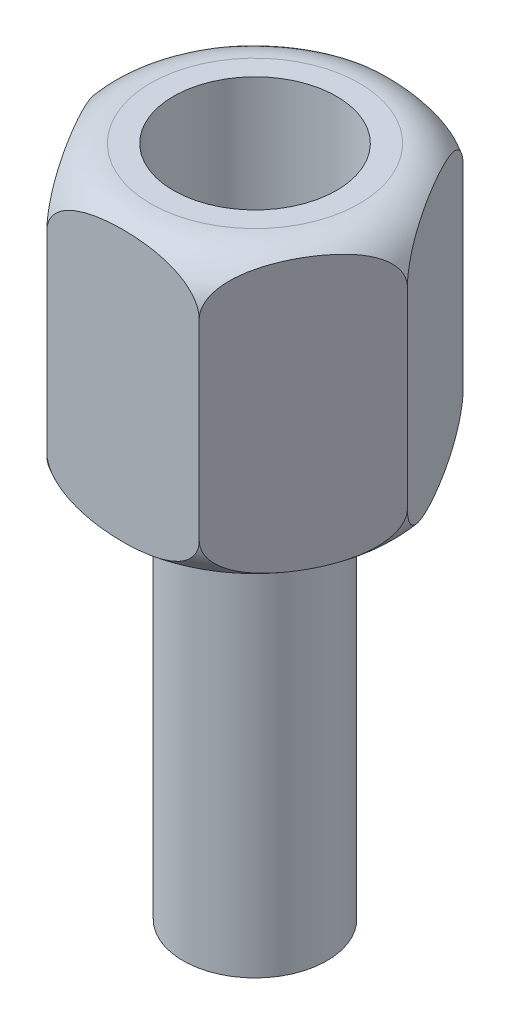
SolidWorks part; units mm, degrees
material "Brass"
ref_plane "Front Plane" through (0, 0, 0) normal (0, 0, 1) x (1, 0, 0)
ref_plane "Top Plane" through (0, 0, 0) normal (0, 1, 0) x (1, 0, 0)
ref_plane "Right Plane" through (0, 0, 0) normal (1, 0, 0) x (0, 0, -1)
sketch "Sketch1" plane through (0, 0, 0) normal (0, 1, 0) x (1, 0, 0)
  line L1 (3.1754, 0) -> (1.5877, 2.75)
  line L2 (1.5877, 2.75) -> (-1.5877, 2.75)
  line L3 (-1.5877, 2.75) -> (-3.1754, 0)
  line L4 (-3.1754, 0) -> (-1.5877, -2.75)
  line L5 (-1.5877, -2.75) -> (1.5877, -2.75)
  line L6 (1.5877, -2.75) -> (3.1754, 0)
  circle A0 centre (0, 0) radius 2.75 construction
  dimension "D1" = 5.5
extrude "Boss-Extrude1" add sketch "Sketch1" along normal blind 6
hole_wizard "M3 Clearance Hole1" positions "Sketch3" profile "Sketch2" hole size "M3" standard "ISO"
sketch "Sketch3" plane through (0, 6, 0) normal (0, 1, 0) x (-1, 0, 0)
  point P0 (0, 0)
sketch "Sketch2" plane through (0, 6, 0) normal (1, 0, 0) x (0, 0, 1)
  line L0 (0, 0) -> (0, 13.0215)
  line L1 (0, 13.0215) -> (1.7, 12)
  line L2 (1.7, 12) -> (1.7, 0)
  line L5 (1.7, 0) -> (0, 0)
  line L10 (0, 13.0215) -> (-1.7, 12) construction
  line L11 (0, -6.35) -> (0, 107.95) construction
  dimension "Hole Dia." = 3.4
  dimension "Hole Depth" = 12
  dimension "Drill Angle" = 118
sketch "Sketch4" plane through (0, 0, 0) normal (0, 0, 1) x (1, 0, 0)
  line L0 (-3.1754, 6) -> (-3.1754, 0) construction
  line L1 (-3.1754, 6) -> (-1.5877, 6) construction
  line L4 (-3.1754, 0) -> (-1.5877, 0) construction
  line L6 (-2.1754, 6) -> (-3.1754, 6)
  line L7 (-3.1754, 6) -> (-3.1754, 5)
  line L8 (-3.1754, 1) -> (-3.1754, 0)
  line L9 (-3.1754, 0) -> (-2.1754, 0)
  line L14 (0, 6) -> (0, 0) construction
  line L15 (-1.5877, 6) -> (1.5877, 6) construction
  arc A0 (-3.1754, 5) -> (-2.1754, 6) centre (-2.1754, 5) cw
  arc A2 (-3.1754, 1) -> (-2.1754, 0) centre (-2.1754, 1) ccw
  dimension "D1" = 1
revolve "Cut-Revolve1" cut sketch "Sketch4" angle 360 about L14
sketch "Sketch5" plane through (0, 0, 0) normal (0, -1, 0) x (1, 0, 0)
  circle A0 centre (0, 0) radius 1.5
  dimension "D1" = 3
extrude "Boss-Extrude2" add sketch "Sketch5" along normal blind 8
